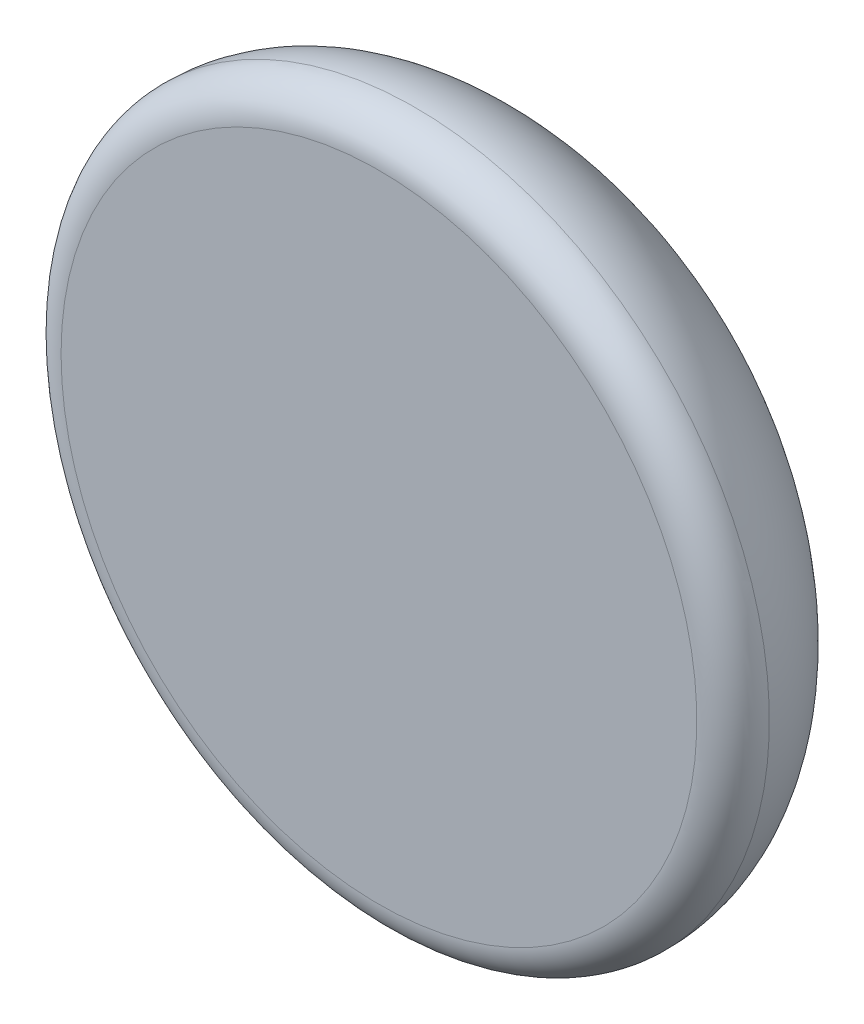
SolidWorks part; units mm, degrees
ref_plane "Front Plane" through (0, 0, 0) normal (0, 0, 1) x (1, 0, 0)
ref_plane "Top Plane" through (0, 0, 0) normal (0, 1, 0) x (1, 0, 0)
ref_plane "Right Plane" through (0, 0, 0) normal (1, 0, 0) x (0, 0, -1)
sketch "Sketch2" plane through (0, 0, 0) normal (0, 1, 0) x (1, 0, 0)
  line L0 (0, 0) -> (-62, 0) construction
  line L1 (0, 33.65) -> (0, 0) construction
  line L2 (0, 0) -> (0, -6.35) construction
  line L3 (-55.65, -6.35) -> (0, -6.35)
  line L4 (0, 33.65) -> (0, -6.35)
  arc A0 (-62, 0) -> (-55.65, -6.35) centre (-55.65, 0) ccw
  ellipse E0 centre (0, 0) end of major axis (-62, 0) minor radius 33.65 (0, 33.65) -> (-62, 0) ccw
  point P11 (0, 0)
  point P12 (0, 0)
  point P13 (-23.8057, 0)
  dimension "D1" = 6.35
  dimension "D2" = 62
  dimension "D3" = 40
revolve "Revolve1" add sketch "Sketch2" angle 360 about L4
